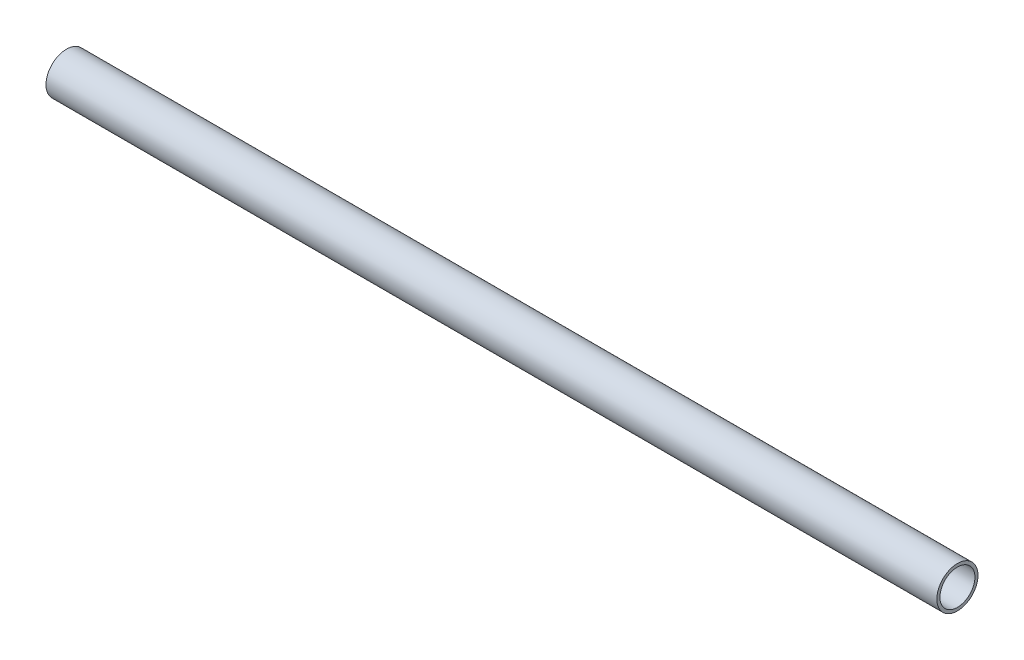
SolidWorks part; units mm, degrees
ref_plane "Front Plane" through (0, 0, 0) normal (0, 0, 1) x (1, 0, 0)
ref_plane "Top Plane" through (0, 0, 0) normal (0, 1, 0) x (1, 0, 0)
ref_plane "Right Plane" through (0, 0, 0) normal (1, 0, 0) x (0, 0, -1)
sketch "Sketch2" plane through (0, 0, 0) normal (1, 0, 0) x (0, 0, -1)
  circle A0 centre (-5.1678, 154.4882) radius 12.7
  circle A1 centre (-5.1678, 154.4882) radius 10.795
  dimension "D1" = 25.4
  dimension "D2" = 21.59
extrude "Boss-Extrude1" add sketch "Sketch2" along normal blind 550
